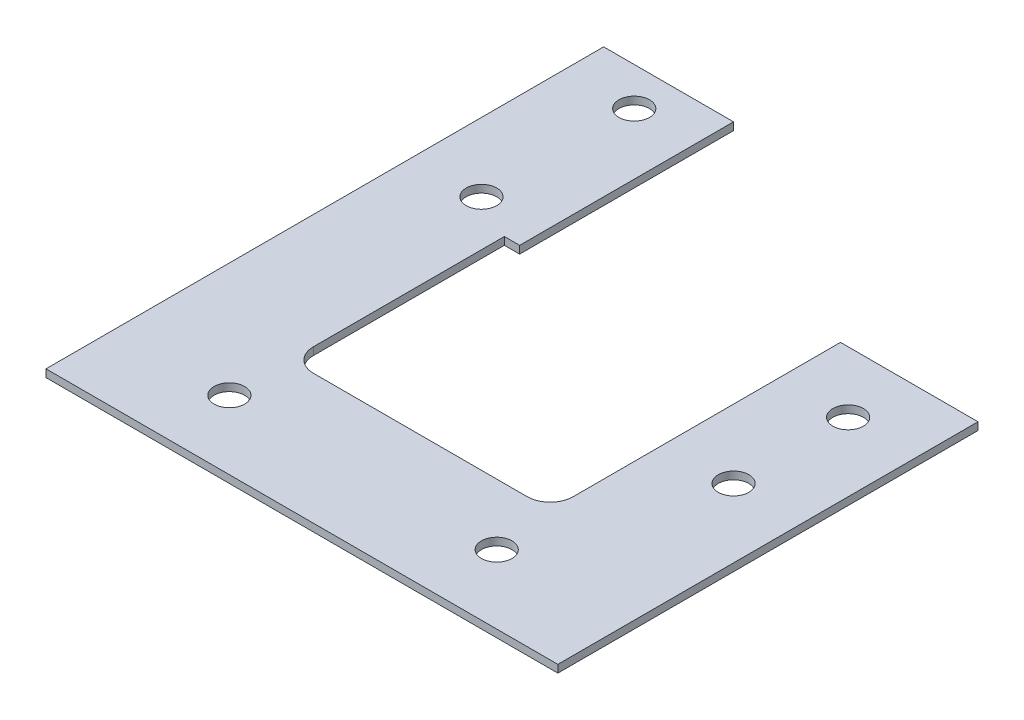
SolidWorks part; units mm, degrees
ref_plane "Front" through (0, 0, 0) normal (0, 0, 1) x (1, 0, 0)
ref_plane "Top" through (0, 0, 0) normal (0, 1, 0) x (1, 0, 0)
ref_plane "Right" through (0, 0, 0) normal (1, 0, 0) x (0, 0, -1)
sketch "Sketch1" plane through (0, 0, 0) normal (0, 1, 0) x (1, 0, 0)
  line L2 (0, 0) -> (0, 40) construction
  line L3 (0, 40) -> (15, 40)
  line L4 (15, 0) -> (15, 40)
  line L6 (0, 40) -> (-3, 40)
  line L7 (-3, 40) -> (-3, 5)
  line L9 (15, 0) -> (15, -15)
  line L10 (15, -15) -> (-52, -15)
  line L11 (-52, -15) -> (-52, 58)
  line L12 (-52, 58) -> (-37, 58)
  line L13 (-37, 30) -> (-37, 5)
  line L15 (-37, 58) -> (-35, 58)
  line L16 (-35, 58) -> (-35, 30)
  line L17 (-35, 30) -> (-37, 30)
  line L18 (-6, 2) -> (-34, 2)
  circle A0 centre (6, 32) radius 2
  circle A1 centre (6, 17) radius 2
  circle A2 centre (-43, 53) radius 2
  circle A3 centre (-43, 33) radius 2
  circle A4 centre (-37, -6) radius 2
  circle A5 centre (-2, -6) radius 2
  arc A6 (-34, 2) -> (-37, 5) centre (-34, 5) cw
  arc A7 (-3, 5) -> (-6, 2) centre (-6, 5) cw
  point P7 (6, 32)
  point P8 (7.5, 40)
  dimension "D3" = 4
  dimension "D13" = 4
  dimension "D20" = 3
  dimension "D21" = 3
  dimension "D1" = 40
  dimension "D2" = 15
  dimension "D4" = 15
  dimension "D5" = 3
  dimension "D6" = 15
  dimension "D7" = 15
  dimension "D8" = 37
  dimension "D9" = 2
  dimension "D10" = 2
  dimension "D11" = 30
  dimension "D12" = 73
  dimension "D14" = 20
  dimension "D15" = 9
  dimension "D16" = 35
  dimension "D17" = 9
  dimension "D18" = 15
  dimension "D19" = 9
  dimension "D22" = 8
extrude "Boss-Extrude2" add sketch "Sketch1" along normal blind 1
equation "\"d_racor\"= 11.8"
equation "\"h_alphasense\"= 5"
equation "\"h_chamber\"= 13"
equation "\"d_alphasense\" = 32.4mm"
equation "\"d_chamber\"= 19"
equation "\"h_base\"= 25 - \"h_chamber\" - \"h_alphasense\"-1"
equation "\"d_thread\"= 2.5"
equation "\"length_thread\"=10"
equation "\"clip_thread_hole\" = 4"
equation "\"clip_thread_tap_drill\" = 3.5"
equation "\"length_racor\"= 10"
equation "\"d_pipe\"=8"
equation "\"D3@Sketch1\"=\"clip_thread_hole\""
equation "\"D13@Sketch1\"=\"clip_thread_hole\""
